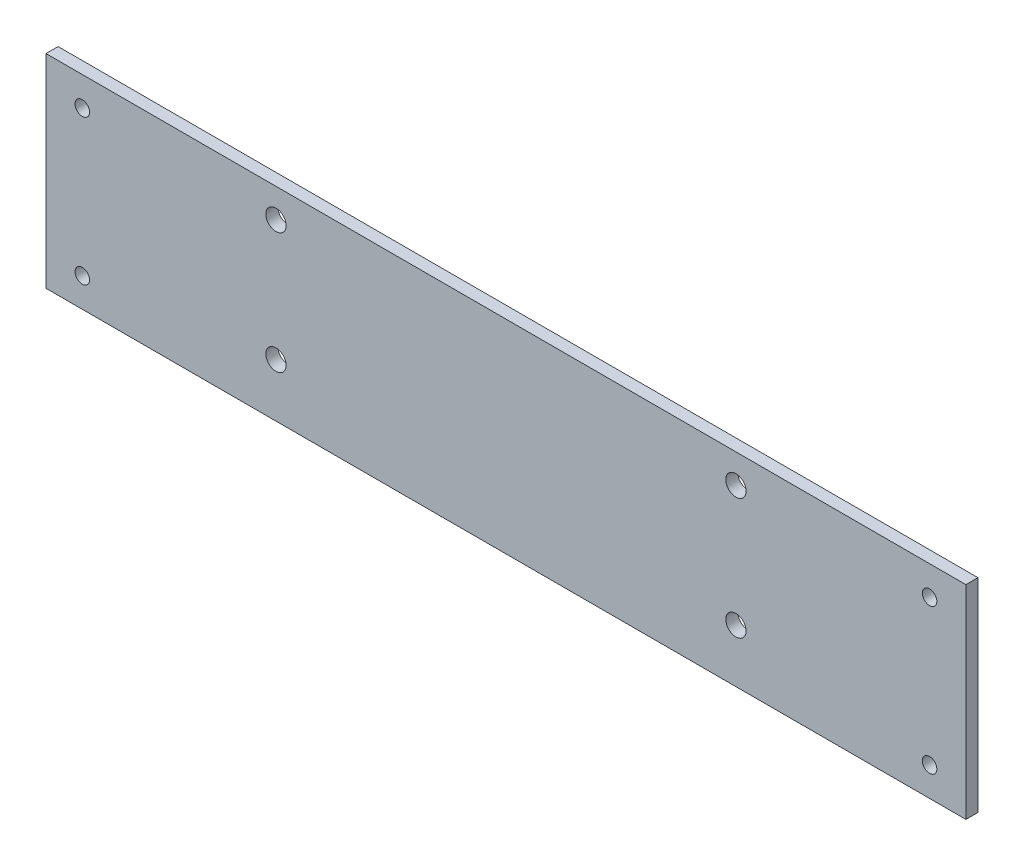
SolidWorks part; units mm, degrees
ref_plane "前视基准面" through (0, 0, 0) normal (0, 0, 1) x (1, 0, 0)
ref_plane "上视基准面" through (0, 0, 0) normal (0, 1, 0) x (1, 0, 0)
ref_plane "右视基准面" through (0, 0, 0) normal (1, 0, 0) x (0, 0, -1)
sketch "Sketch1" plane through (0, 0, 0) normal (0, 0, 1) x (1, 0, 0)
  line L0 (-129.2259, 82.1397) -> (-129.2259, -62.8603) construction
  line L1 (-129.2259, 44.0673) -> (60.7741, 44.0673)
  line L2 (-129.2259, 44.0673) -> (-129.2259, -5.9327)
  line L3 (-129.2259, -5.9327) -> (60.7741, -5.9327)
  line L4 (60.7741, 44.0673) -> (60.7741, -5.9327)
  line L5 (60.7741, 82.1397) -> (60.7741, -62.8603) construction
  dimension "D2" = 50
  dimension "D3" = 0
  dimension "D4" = 0
extrude "Boss-Extrude1" add sketch "Sketch1" along normal blind 2.5
sketch "Sketch2" plane through (0, 0, 2.5) normal (0, 0, 1) x (1, 0, 0)
  line L0 (-129.2259, 44.0673) -> (-129.2259, -5.9327) construction
  line L1 (60.7741, -5.9327) -> (60.7741, 44.0673) construction
  line L2 (60.7741, 44.0673) -> (-129.2259, 44.0673) construction
  line L3 (-129.2259, -5.9327) -> (60.7741, -5.9327) construction
  circle A0 centre (-121.7259, 34.0673) radius 1.5
  circle A1 centre (-121.7259, 4.0673) radius 1.5
  circle A2 centre (53.2741, 34.0673) radius 1.5
  circle A3 centre (53.2741, 4.0673) radius 1.5
  dimension "D1" = 3
  dimension "D2" = 3
  dimension "D3" = 3
  dimension "D4" = 3
  dimension "D5" = 7.5
  dimension "D6" = 7.5
  dimension "D8" = 7.5
  dimension "D9" = 10
  dimension "D10" = 10
  dimension "D11" = 10
  dimension "D12" = 10
  dimension "D7" = 7.5
extrude "Cut-Extrude1" cut sketch "Sketch2" against normal through all
sketch "Sketch3" plane through (0, 0, 2.5) normal (0, 0, 1) x (1, 0, 0)
  line L0 (60.7741, 44.0673) -> (-129.2259, 44.0673) construction
  line L1 (-129.2259, 44.0673) -> (-129.2259, -5.9327) construction
  circle A0 centre (-81.7259, 34.0673) radius 2.1
  circle A1 centre (13.2741, 34.0673) radius 2.1
  circle A2 centre (13.2741, 9.0673) radius 2.1
  circle A3 centre (-81.7259, 9.0673) radius 2.1
  dimension "D1" = 4.2
  dimension "D2" = 25
  dimension "D3" = 95
  dimension "D4" = 95
  dimension "D5" = 25
  dimension "D6" = 4.2
  dimension "D7" = 4.2
  dimension "D8" = 4.2
  dimension "D9" = 10
  dimension "D10" = 47.5
  dimension "D11" = 47.5
extrude "Cut-Extrude2" cut sketch "Sketch3" against normal through all
sketch "草图2" plane through (0, 0, 2.5) normal (0, 0, 1) x (1, 0, 0)
  line L0 (-129.2259, 44.0673) -> (-129.2259, -5.9327) construction
  line L1 (-129.2259, 40.0673) -> (60.7741, 40.0673)
  line L2 (-129.2259, 40.0673) -> (-129.2259, -1.9327)
  line L3 (-129.2259, -1.9327) -> (60.7741, -1.9327)
  line L4 (60.7741, 40.0673) -> (60.7741, -1.9327)
  line L5 (60.7741, -5.9327) -> (60.7741, 44.0673) construction
  line L6 (60.7741, 44.0673) -> (-129.2259, 44.0673) construction
  line L7 (-132.726, 50.2016) -> (67.229, 50.2016)
  line L8 (-132.726, 50.2016) -> (-132.726, -10.5946)
  line L9 (-132.726, -10.5946) -> (67.229, -10.5946)
  line L10 (67.229, 50.2016) -> (67.229, -10.5946)
  line L11 (-129.2259, -5.9327) -> (60.7741, -5.9327) construction
  dimension "D1" = 4
  dimension "D2" = 4
extrude "切除-拉伸1" cut sketch "草图2" against normal blind 10
